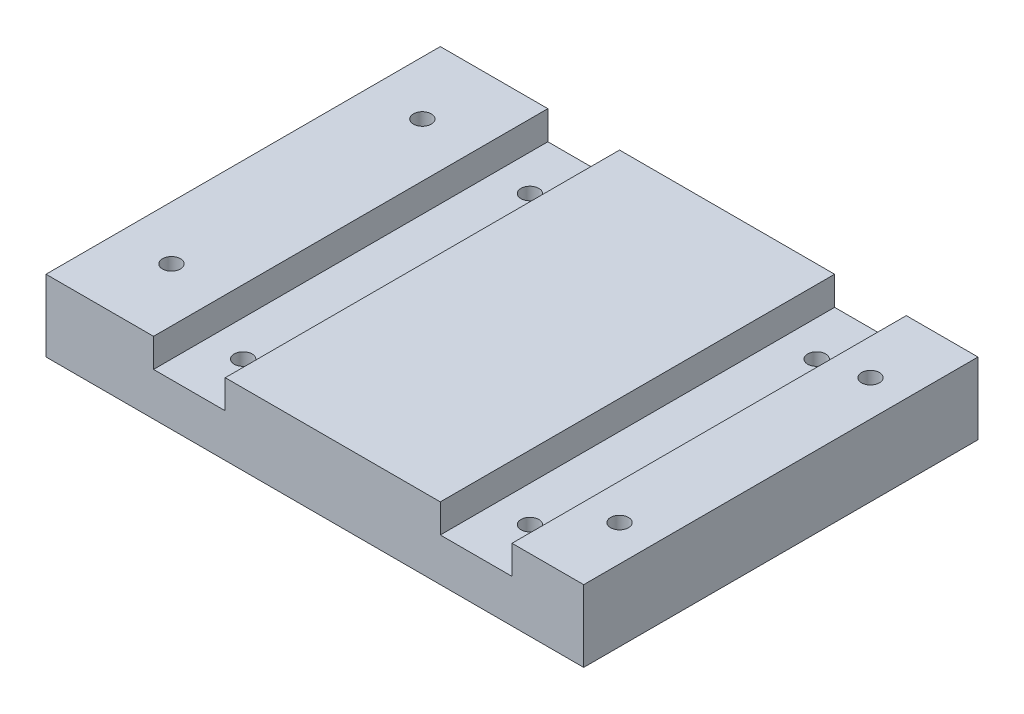
SolidWorks part; units mm, degrees
material "1060 Alloy"
ref_plane "Front Plane" through (0, 0, 0) normal (0, 0, 1) x (1, 0, 0)
ref_plane "Top Plane" through (0, 0, 0) normal (0, 1, 0) x (1, 0, 0)
ref_plane "Right Plane" through (0, 0, 0) normal (1, 0, 0) x (0, 0, -1)
sketch "Sketch1" plane through (0, 0, 0) normal (0, 0, 1) x (1, 0, 0)
  line L0 (-74.4141, 0) -> (75.5859, 0)
  line L1 (75.5859, 0) -> (75.5859, 20)
  line L2 (75.5859, 20) -> (55.5859, 20)
  line L3 (55.5859, 20) -> (55.5859, 12)
  line L4 (55.5859, 12) -> (35.5859, 12)
  line L5 (35.5859, 12) -> (35.5859, 20)
  line L6 (35.5859, 20) -> (-24.4141, 20)
  line L7 (-24.4141, 20) -> (-24.4141, 12)
  line L8 (-24.4141, 12) -> (-44.4141, 12)
  line L9 (-44.4141, 12) -> (-44.4141, 20)
  line L10 (-44.4141, 20) -> (-74.4141, 20)
  line L11 (-74.4141, 20) -> (-74.4141, 0)
  dimension "D1" = 150
  dimension "D2" = 20
  dimension "D3" = 20
  dimension "D4" = 20
  dimension "D5" = 20
  dimension "D6" = 60
  dimension "D7" = 20
  dimension "D8" = 12
extrude "Boss-Extrude1" add sketch "Sketch1" along normal blind 110
sketch "Sketch2" plane through (0, 20, 0) normal (0, 1, 0) x (1, 0, 0)
  line L0 (-44.4141, 0) -> (-74.4141, 0) construction
  line L1 (-74.4141, -110) -> (-74.4141, 0) construction
  line L2 (75.5859, -110) -> (75.5859, 0) construction
  line L4 (-44.4141, -110) -> (-74.4141, -110) construction
  line L5 (75.5859, -110) -> (55.5859, -110) construction
  point P0 (65.5859, -20)
  point P1 (65.5859, -90)
  point P2 (-59.4141, -90)
  point P3 (-59.4141, -20)
  dimension "D1" = 20
  dimension "D2" = 15
  dimension "D3" = 10
  dimension "D4" = 15
  dimension "D5" = 20
  dimension "D6" = 20
  dimension "D7" = 10
hole_wizard "Ø5.0mm Dowel Hole1" positions "3DSketch1" profile "Sketch3" hole size "Ø5.0" standard "ANSI Metric" end condition through all
sketch3d "3DSketch1"
  point P0 (-59.4141, 20, 20)
  point P3 (-59.4141, 20, 90)
  point P6 (65.5859, 20, 20)
  point P9 (65.5859, 20, 90)
sketch "Sketch3" plane through (-59.4141, 20, 20) normal (1, 0, 0) x (0, 0, 1)
  line L0 (0, 0) -> (0, 20)
  line L1 (0, 20) -> (2.5, 20)
  line L2 (2.5, 20) -> (2.5, 0)
  line L5 (2.5, 0) -> (0, 0)
  line L11 (0, -6.35) -> (0, 107.95) construction
  dimension "Thru Hole Dia." = 5
  dimension "Thru Hole Depth" = 20
sketch "Sketch4" plane through (0, 12, 0) normal (0, 1, 0) x (1, 0, 0)
  line L0 (55.5859, 0) -> (35.5859, 0) construction
  line L1 (35.5859, -110) -> (35.5859, 0) construction
  line L2 (55.5859, -110) -> (55.5859, 0) construction
  line L3 (55.5859, -110) -> (35.5859, -110) construction
  point P0 (45.5859, -15)
  point P1 (45.5859, -95)
  point P10 (-34.4141, -15)
  point P11 (-34.4141, -95)
  dimension "D1" = 15
  dimension "D2" = 10
  dimension "D3" = 10
  dimension "D4" = 15
hole_wizard "Ø5.0mm Dowel Hole2" positions "3DSketch2" profile "Sketch5" hole size "Ø5.0" standard "ANSI Metric" end condition up to next
sketch3d "3DSketch2"
  point P0 (-34.4141, 12, 15)
  point P3 (-34.4141, 12, 95)
  point P6 (45.5859, 12, 15)
  point P9 (45.5859, 12, 95)
sketch "Sketch5" plane through (-34.4141, 12, 15) normal (1, 0, 0) x (0, 0, 1)
  line L0 (0, 0) -> (0, 12)
  line L1 (0, 12) -> (2.5, 12)
  line L2 (2.5, 12) -> (2.5, 0)
  line L5 (2.5, 0) -> (0, 0)
  line L11 (0, -6.35) -> (0, 107.95) construction
  dimension "Thru Hole Dia." = 5
  dimension "Thru Hole Depth" = 12
